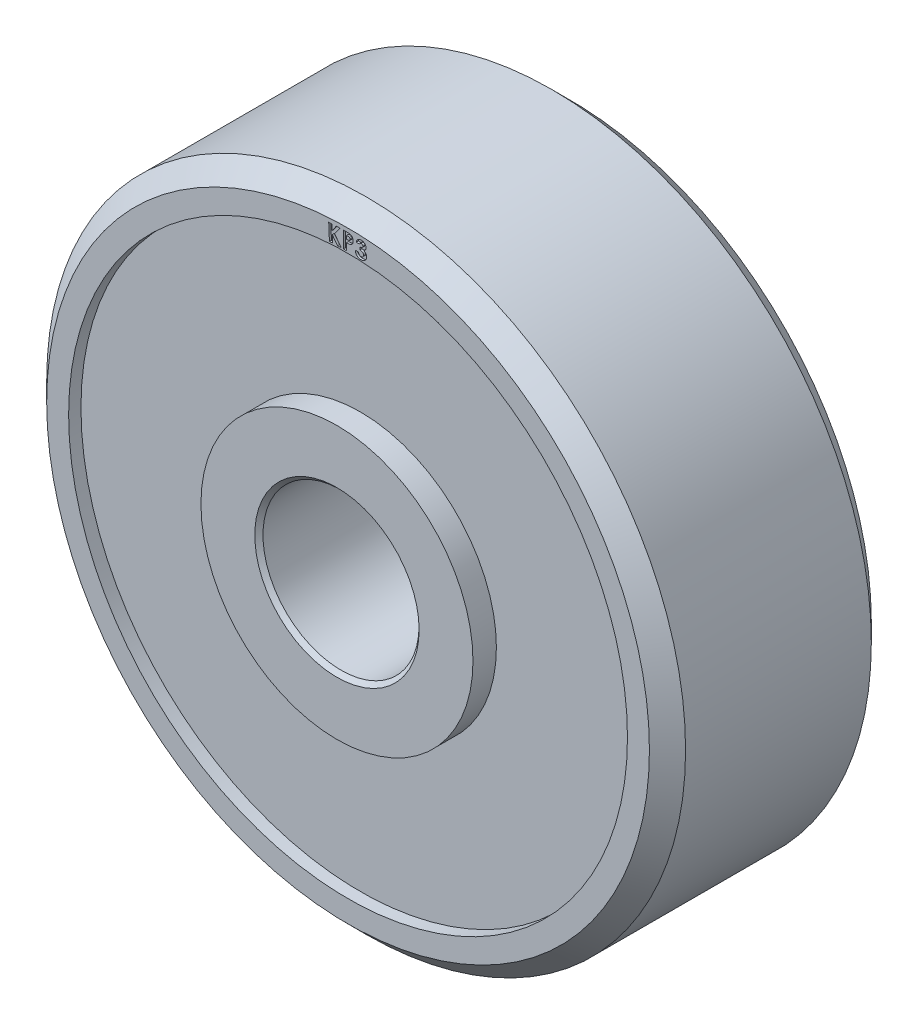
SolidWorks part; units mm, degrees
ref_plane "Front Plane" through (0, 0, 0) normal (0, 0, 1) x (1, 0, 0)
ref_plane "Top Plane" through (0, 0, 0) normal (0, 1, 0) x (1, 0, 0)
ref_plane "Right Plane" through (0, 0, 0) normal (1, 0, 0) x (0, 0, -1)
sketch "Sketch1" plane through (0, 0, 0) normal (1, 0, 0) x (0, 0, -1)
  line L0 (0, 0) -> (6.5272, 0) construction
  line L1 (-3.7719, 2.54) -> (-3.7719, 4.2037)
  line L2 (-3.7719, 4.2037) -> (-3.048, 4.2037)
  line L3 (-3.048, 4.2037) -> (-3.048, 8.636)
  line L4 (-3.048, 8.636) -> (-3.429, 8.636)
  line L5 (-3.429, 8.636) -> (-3.429, 9.3142)
  line L6 (-3.429, 9.3142) -> (-2.8702, 9.873)
  line L7 (-2.8702, 9.873) -> (2.8702, 9.873)
  line L8 (-3.6449, 2.413) -> (3.6449, 2.413)
  line L9 (0, 0) -> (0, 14.7344) construction
  line L10 (3.429, 9.3142) -> (2.8702, 9.873)
  line L11 (3.429, 8.636) -> (3.429, 9.3142)
  line L12 (3.048, 8.636) -> (3.429, 8.636)
  line L13 (3.048, 4.2037) -> (3.048, 8.636)
  line L14 (3.7719, 4.2037) -> (3.048, 4.2037)
  line L15 (3.7719, 2.54) -> (3.7719, 4.2037)
  line L16 (-3.7719, 2.54) -> (-3.6449, 2.413)
  line L17 (3.6449, 2.413) -> (3.7719, 2.54)
  point P3 (-3.7719, 2.413)
  point P19 (3.7719, 2.413)
  dimension "D1" = 4.826
  dimension "D2" = 8.4074
  dimension "D3" = 7.5438
  dimension "D4" = 6.858
  dimension "D5" = 0.381
  dimension "D6" = 17.272
  dimension "D7" = 45
  dimension "D8" = 0.5588
  dimension "D9" = 19.746
revolve "Revolve1" add sketch "Sketch1" angle 360 about L0
sketch "Sketch2" plane through (0, 0, 3.429) normal (0, 0, 1) x (1, 0, 0)
  line L0 (0, 0) -> (0, 8.6868) construction
  arc A0 (-0.6344, 8.6636) -> (0.6344, 8.6636) centre (0, 0) cw construction
  text T0 "KP3" font "Century Gothic" height 0.508
  dimension "D1" = 8.6868
  dimension "D2" = 1.27
extrude "Cut-Extrude1" cut sketch "Sketch2" against normal blind 0.0635
